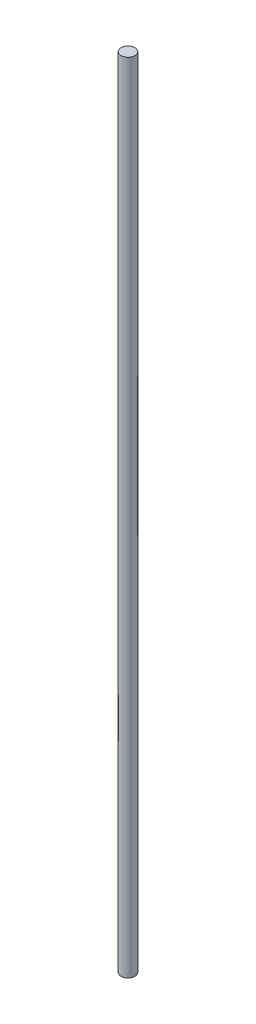
SolidWorks part; units mm, degrees
material "2024 Alloy"
ref_plane "Front Plane" through (0, 0, 0) normal (0, 0, 1) x (1, 0, 0)
ref_plane "Top Plane" through (0, 0, 0) normal (0, 1, 0) x (1, 0, 0)
ref_plane "Right Plane" through (0, 0, 0) normal (1, 0, 0) x (0, 0, -1)
sketch "Sketch1" plane through (0, 0, 0) normal (0, 1, 0) x (1, 0, 0)
  circle A0 centre (0, 0) radius 7.9375
extrude "Boss-Extrude1" add sketch "Sketch1" along normal blind 914.4
